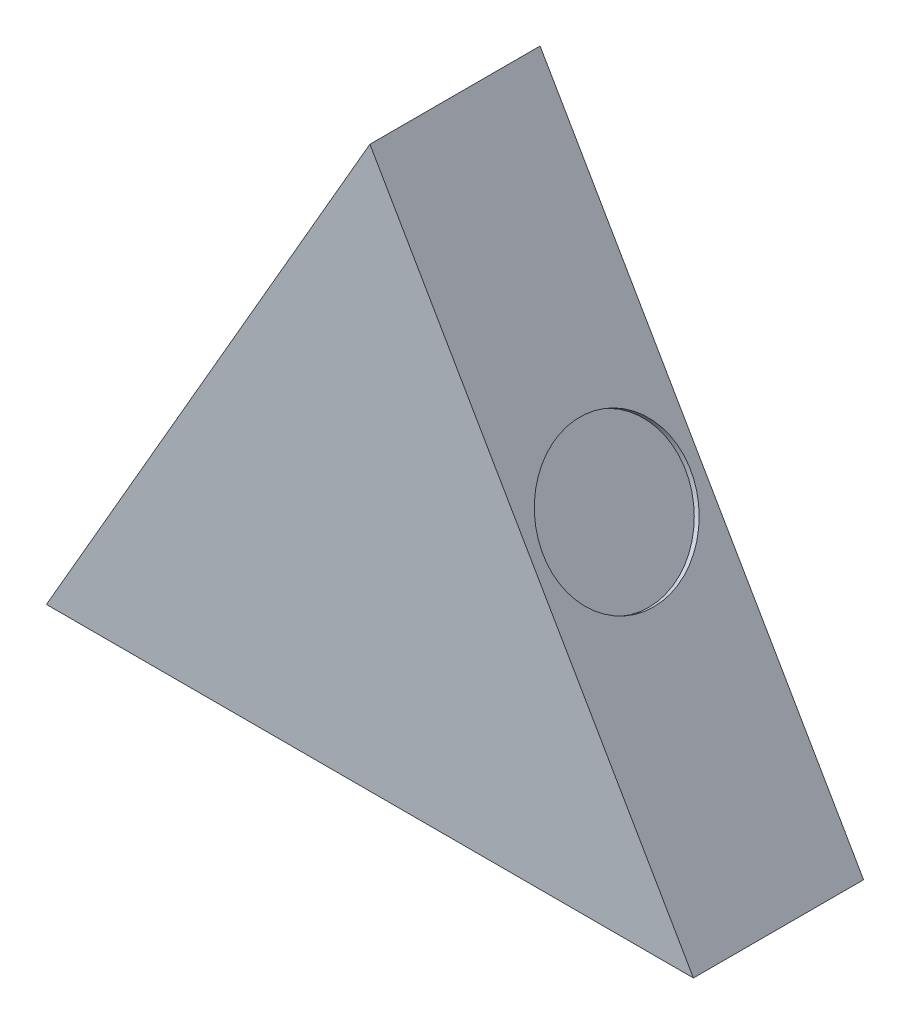
SolidWorks part; units mm, degrees
ref_plane "前视基准面" through (0, 0, 0) normal (0, 0, 1) x (1, 0, 0)
ref_plane "上视基准面" through (0, 0, 0) normal (0, 1, 0) x (1, 0, 0)
ref_plane "右视基准面" through (0, 0, 0) normal (1, 0, 0) x (0, 0, -1)
other "Configuration Table"
sketch "草图1" plane through (0, 0, 0) normal (0, 0, 1) x (1, 0, 0)
  line L0 (0, 0) -> (0, 24.6971) construction
  line L1 (0, 24.6971) -> (-28.5178, -24.6971)
  line L2 (-28.5178, -24.6971) -> (28.5178, -24.6971)
  line L3 (28.5178, -24.6971) -> (0, 24.6971)
extrude "凸台-拉伸2" add sketch "草图1" along normal blind 15
sketch "草图4" plane through (0, 0, 0) normal (0, 0, 1) x (1, 0, 0)
  line L0 (-13.4738, -3.563) -> (-13.4738, -20.063)
  line L1 (-10, -23.5368) -> (10, -23.5368)
  line L2 (13.4738, -3.563) -> (13.4738, -20.063)
  line L3 (-2.3763, 9.7004) -> (-3.4178, 9.4701)
  line L4 (2.3763, 9.7004) -> (3.4178, 9.4701)
  arc A0 (2.3763, 9.7004) -> (-2.3763, 9.7004) centre (0, 6.581) ccw
  arc A1 (-13.4738, -20.063) -> (-10, -23.5368) centre (-10, -20.063) ccw
  arc A2 (10, -23.5368) -> (13.4738, -20.063) centre (10, -20.063) ccw
  arc A3 (13.4738, -3.563) -> (3.4178, 9.4701) centre (0, -3.563) ccw
  arc A4 (-3.4178, 9.4701) -> (-13.4738, -3.563) centre (0, -3.563) ccw
extrude "切除-拉伸2" cut sketch "草图4" along normal blind 13
sketch "草图5" plane through (0, -24.6971, 0) normal (0, -1, 0) x (1, 0, 0)
  line L0 (0, 15) -> (0, 0) construction
  line L1 (-28.5178, 15) -> (28.5178, 15) construction
  circle A0 centre (0, 7.5) radius 6.5
  dimension "D1" = 13
sketch "草图6" plane through (-14.2589, 0, 0) normal (0.866, -0.5, 0) x (0.5, 0.866, 0)
  line L0 (0, 15) -> (0, 0) construction
  circle A0 centre (0, 7.5) radius 6.5
sketch "草图7" plane through (14.2589, 0, 0) normal (-0.866, -0.5, 0) x (0.5, -0.866, 0)
  line L0 (0, 15) -> (0, 0) construction
  circle A0 centre (0, 7.5) radius 6.5
extrude "切除-拉伸3" cut sketch "草图5" against normal blind 0.5
extrude "切除-拉伸5" cut sketch "草图6" along normal blind 0.5
extrude "切除-拉伸8" cut sketch "草图7" along normal blind 0.5
